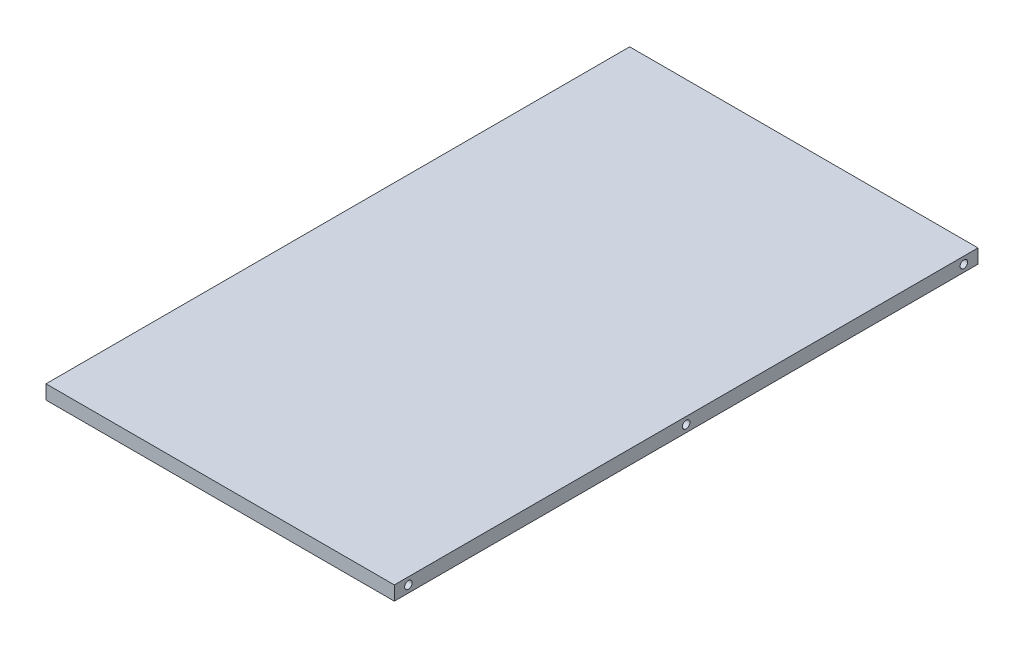
SolidWorks part; units mm, degrees
material "Oak"
ref_plane "Front Plane" through (0, 0, 0) normal (0, 0, 1) x (1, 0, 0)
ref_plane "Top Plane" through (0, 0, 0) normal (0, 1, 0) x (1, 0, 0)
ref_plane "Right Plane" through (0, 0, 0) normal (1, 0, 0) x (0, 0, -1)
sketch "Sketch1" plane through (0, 0, 0) normal (0, 1, 0) x (1, 0, 0)
  line L1 (-185, -310) -> (185, -310)
  line L2 (-185, -310) -> (-185, 310)
  line L3 (-185, 310) -> (185, 310)
  line L4 (185, -310) -> (185, 310)
  line L5 (-185, -310) -> (185, 310) construction
  line L6 (-185, 310) -> (185, -310) construction
  point P0 (0, 0)
  dimension "D1" = 370
  dimension "D2" = 620
extrude "Boss-Extrude1" add sketch "Sketch1" along normal blind 15
sketch "Sketch2" plane through (0, 0, 0) normal (0, -1, 0) x (1, 0, 0)
  line L0 (0, 0) -> (0, 310) construction
  line L1 (-185, 310) -> (185, 310) construction
  line L2 (0, 0) -> (185, 0) construction
  line L3 (185, 310) -> (185, -310) construction
  circle A0 centre (160, 285) radius 20 construction
  circle A1 centre (160, 285) radius 2.5
  circle A2 centre (-160, 285) radius 2.5
  circle A3 centre (-160, -285) radius 2.5
  circle A4 centre (160, -285) radius 2.5
  dimension "D1" = 40
  dimension "D4" = 5
  dimension "D2" = 25
  dimension "D3" = 25
extrude "Cut-Extrude1" cut sketch "Sketch2" against normal blind 2
sketch "Sketch5" plane through (-185, 0, 0) normal (-1, 0, 0) x (0, 0, 1)
  line L0 (-310, 15) -> (-310, 0) construction
  line L1 (-310, 7.5) -> (-299, 7.5) construction
  line L2 (295, 15) -> (295, 0) construction
  line L3 (-310, 15) -> (310, 15) construction
  line L4 (-310, 0) -> (310, 0) construction
  line L5 (310, 15) -> (310, 0) construction
  circle A0 centre (-295, 7.5) radius 4
  point P4 (-310, 7.5)
  dimension "D1" = 8
  dimension "D2" = 11
  dimension "D3" = 15
extrude "Cut-Extrude2" cut sketch "Sketch5" against normal blind 10
pattern_linear "LPattern1" count 3 spacing 295 along (0, 0, 1) of "Cut-Extrude2"
mirror "Mirror1" about plane through (0, 0, 0) normal (1, 0, 0) of "LPattern1", "Cut-Extrude2"
sketch "Sketch6" plane through (0, 0, -310) normal (0, 0, -1) x (-1, 0, 0)
  line L0 (-185, 7.5) -> (-174, 7.5) construction
  line L1 (-185, 15) -> (-185, 0) construction
  line L2 (170, 15) -> (170, 0) construction
  line L3 (-185, 15) -> (185, 15) construction
  line L4 (-185, 0) -> (185, 0) construction
  line L5 (185, 15) -> (185, 0) construction
  circle A0 centre (-170, 7.5) radius 4
  dimension "D1" = 8
  dimension "D2" = 11
  dimension "D3" = 15
extrude "Cut-Extrude4" cut sketch "Sketch6" against normal blind 10
pattern_linear "LPattern2" count 3 spacing 170 along (-1, 0, 0) of "Cut-Extrude4"
equation "\"A\"= 40cm - ( 2 * \"D\" )"
equation "\"B\"= 75cm - 10cm - ( 2 * \"D\" )"
equation "\"C\"= 70cm"
equation "\"D1@Sketch1\"=\"A\""
equation "\"D2@Sketch1\"=\"B\""
equation "\"D\"= 15mm"
equation "\"D1@Boss-Extrude1\"=\"D\""
